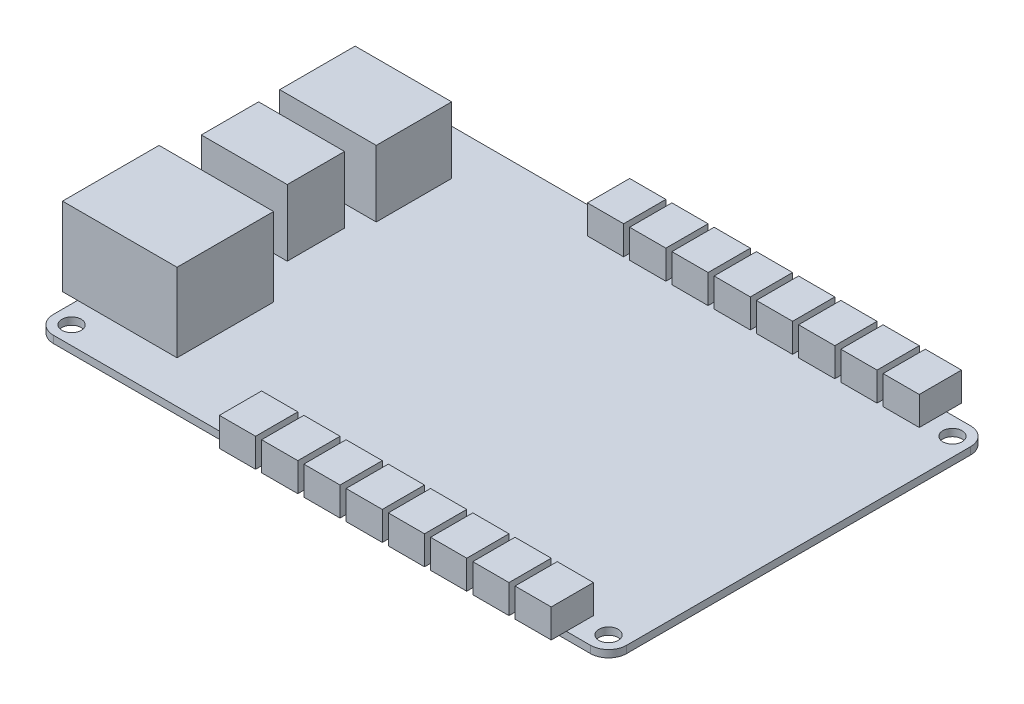
SolidWorks part; units mm, degrees
ref_plane "Front Plane" through (0, 0, 0) normal (0, 0, 1) x (1, 0, 0)
ref_plane "Top Plane" through (0, 0, 0) normal (0, 1, 0) x (1, 0, 0)
ref_plane "Right Plane" through (0, 0, 0) normal (1, 0, 0) x (0, 0, -1)
sketch "Sketch1" plane through (0, 0, 0) normal (0, 1, 0) x (1, 0, 0)
  line L1 (-54.7675, 6.7441) -> (34.2325, 6.7441)
  line L2 (-57.7675, 3.7441) -> (-57.7675, -53.2559)
  line L3 (-54.7675, -56.2559) -> (34.2325, -56.2559)
  line L4 (37.2325, 3.7441) -> (37.2325, -53.2559)
  arc A0 (-57.7675, -53.2559) -> (-54.7675, -56.2559) centre (-54.7675, -53.2559) ccw
  arc A1 (34.2325, -56.2559) -> (37.2325, -53.2559) centre (34.2325, -53.2559) ccw
  arc A2 (34.2325, 6.7441) -> (37.2325, 3.7441) centre (34.2325, 3.7441) cw
  arc A3 (-54.7675, 6.7441) -> (-57.7675, 3.7441) centre (-54.7675, 3.7441) ccw
  circle A4 centre (-54.7675, 3.7441) radius 1.6
  circle A5 centre (-54.7675, -53.2559) radius 1.6
  circle A6 centre (34.2325, -53.2559) radius 1.6
  circle A7 centre (34.2325, 3.7441) radius 1.6
  point P6 (-57.7675, -56.2559)
  point P9 (37.2325, -56.2559)
  point P14 (-57.7675, 6.7441)
  dimension "D3" = 3
  dimension "D4" = 3.2
  dimension "D5" = 3.2
  dimension "D6" = 3.2
  dimension "D7" = 3.2
  dimension "D1" = 95
  dimension "D2" = 63
extrude "pcb" add sketch "Sketch1" along normal blind 1.2
sketch "Sketch2" plane through (0, 1.2, 0) normal (0, 1, 0) x (1, 0, 0)
  line L0 (-17.7675, -51.7559) -> (-17.7675, -58.7559)
  line L1 (-24.7675, -51.7559) -> (-18.7675, -51.7559)
  line L2 (-24.7675, -51.7559) -> (-24.7675, -58.7559)
  line L3 (-24.7675, -58.7559) -> (-18.7675, -58.7559)
  line L4 (-18.7675, -51.7559) -> (-18.7675, -58.7559)
  line L5 (-17.7675, -51.7559) -> (-11.7675, -51.7559)
  line L6 (-11.7675, -51.7559) -> (-11.7675, -58.7559)
  line L7 (-17.7675, -58.7559) -> (-11.7675, -58.7559)
  line L8 (-10.7675, -51.7559) -> (-10.7675, -58.7559)
  line L9 (-10.7675, -51.7559) -> (-4.7675, -51.7559)
  line L10 (-4.7675, -51.7559) -> (-4.7675, -58.7559)
  line L11 (-10.7675, -58.7559) -> (-4.7675, -58.7559)
  line L12 (-3.7675, -51.7559) -> (-3.7675, -58.7559)
  line L13 (-3.7675, -51.7559) -> (2.2325, -51.7559)
  line L14 (2.2325, -51.7559) -> (2.2325, -58.7559)
  line L15 (-3.7675, -58.7559) -> (2.2325, -58.7559)
  line L16 (3.2325, -51.7559) -> (3.2325, -58.7559)
  line L17 (3.2325, -51.7559) -> (9.2325, -51.7559)
  line L18 (9.2325, -51.7559) -> (9.2325, -58.7559)
  line L19 (3.2325, -58.7559) -> (9.2325, -58.7559)
  line L20 (10.2325, -51.7559) -> (10.2325, -58.7559)
  line L21 (10.2325, -51.7559) -> (16.2325, -51.7559)
  line L22 (16.2325, -51.7559) -> (16.2325, -58.7559)
  line L23 (10.2325, -58.7559) -> (16.2325, -58.7559)
  line L24 (17.2325, -51.7559) -> (17.2325, -58.7559)
  line L25 (17.2325, -51.7559) -> (23.2325, -51.7559)
  line L26 (23.2325, -51.7559) -> (23.2325, -58.7559)
  line L27 (17.2325, -58.7559) -> (23.2325, -58.7559)
  line L28 (24.2325, -51.7559) -> (24.2325, -58.7559)
  line L29 (24.2325, -51.7559) -> (30.2325, -51.7559)
  line L30 (30.2325, -51.7559) -> (30.2325, -58.7559)
  line L31 (24.2325, -58.7559) -> (30.2325, -58.7559)
  line L32 (-57.7675, 3.7441) -> (-57.7675, -53.2559) construction
  line L33 (-54.7675, -56.2559) -> (34.2325, -56.2559) construction
  line L34 (-57.7675, -24.7559) -> (37.2325, -24.7559) construction
  line L35 (37.2325, -53.2559) -> (37.2325, 3.7441) construction
  line L36 (24.2325, 9.2441) -> (30.2325, 9.2441)
  line L37 (30.2325, 2.2441) -> (30.2325, 9.2441)
  line L38 (24.2325, 2.2441) -> (30.2325, 2.2441)
  line L39 (24.2325, 2.2441) -> (24.2325, 9.2441)
  line L40 (17.2325, 9.2441) -> (23.2325, 9.2441)
  line L41 (23.2325, 2.2441) -> (23.2325, 9.2441)
  line L42 (17.2325, 2.2441) -> (23.2325, 2.2441)
  line L43 (17.2325, 2.2441) -> (17.2325, 9.2441)
  line L44 (10.2325, 9.2441) -> (16.2325, 9.2441)
  line L45 (16.2325, 2.2441) -> (16.2325, 9.2441)
  line L46 (10.2325, 2.2441) -> (16.2325, 2.2441)
  line L47 (10.2325, 2.2441) -> (10.2325, 9.2441)
  line L48 (3.2325, 9.2441) -> (9.2325, 9.2441)
  line L49 (9.2325, 2.2441) -> (9.2325, 9.2441)
  line L50 (3.2325, 2.2441) -> (9.2325, 2.2441)
  line L51 (3.2325, 2.2441) -> (3.2325, 9.2441)
  line L52 (-3.7675, 9.2441) -> (2.2325, 9.2441)
  line L53 (2.2325, 2.2441) -> (2.2325, 9.2441)
  line L54 (-3.7675, 2.2441) -> (2.2325, 2.2441)
  line L55 (-3.7675, 2.2441) -> (-3.7675, 9.2441)
  line L56 (-10.7675, 9.2441) -> (-4.7675, 9.2441)
  line L57 (-4.7675, 2.2441) -> (-4.7675, 9.2441)
  line L58 (-10.7675, 2.2441) -> (-4.7675, 2.2441)
  line L59 (-10.7675, 2.2441) -> (-10.7675, 9.2441)
  line L60 (-17.7675, 9.2441) -> (-11.7675, 9.2441)
  line L61 (-11.7675, 2.2441) -> (-11.7675, 9.2441)
  line L62 (-17.7675, 2.2441) -> (-11.7675, 2.2441)
  line L63 (-18.7675, 2.2441) -> (-18.7675, 9.2441)
  line L64 (-24.7675, 9.2441) -> (-18.7675, 9.2441)
  line L65 (-24.7675, 2.2441) -> (-24.7675, 9.2441)
  line L66 (-24.7675, 2.2441) -> (-18.7675, 2.2441)
  line L67 (-17.7675, 2.2441) -> (-17.7675, 9.2441)
  dimension "D1" = 6
  dimension "D2" = 7
  dimension "D4" = 33
  dimension "D5" = 2.5
  dimension "D3" = 8
extrude "pop connectors" add sketch "Sketch2" along normal blind 4.75
sketch "usb" plane through (0, 1.2, 0) normal (0, 1, 0) x (1, 0, 0)
  line L0 (-54.7675, -56.2559) -> (-24.7675, -56.2559) construction
  line L1 (-60.2675, -0.7559) -> (-44.2675, -0.7559)
  line L2 (-60.2675, -0.7559) -> (-60.2675, -13.2559)
  line L3 (-60.2675, -13.2559) -> (-44.2675, -13.2559)
  line L4 (-44.2675, -0.7559) -> (-44.2675, -13.2559)
  line L5 (-57.7675, 3.7441) -> (-57.7675, -53.2559) construction
  dimension "D1" = 43
  dimension "D2" = 2.5
  dimension "D3" = 16
  dimension "D4" = 12.5
extrude "USB B" add sketch "usb" along normal blind 11
sketch "Sketch4" plane through (0, 1.2, 0) normal (0, 1, 0) x (1, 0, 0)
  line L0 (-54.7675, -56.2559) -> (-24.7675, -56.2559) construction
  line L1 (-60.2675, -16.7559) -> (-46.0175, -16.7559)
  line L2 (-60.2675, -16.7559) -> (-60.2675, -26.2559)
  line L3 (-60.2675, -26.2559) -> (-46.0175, -26.2559)
  line L4 (-46.0175, -16.7559) -> (-46.0175, -26.2559)
  line L5 (-57.7675, -13.2559) -> (-57.7675, -53.2559) construction
  dimension "D1" = 9.5
  dimension "D2" = 14.25
  dimension "D3" = 30
  dimension "D4" = 2.5
extrude "DC power" add sketch "Sketch4" along normal blind 11
sketch "Sketch5" plane through (0, 1.2, 0) normal (0, 1, 0) x (1, 0, 0)
  line L0 (-54.7675, -56.2559) -> (-24.7675, -56.2559) construction
  line L1 (-60.2675, -33.2559) -> (-41.2852, -33.2559)
  line L2 (-60.2675, -33.2559) -> (-60.2675, -49.2559)
  line L3 (-60.2675, -49.2559) -> (-41.2852, -49.2559)
  line L4 (-41.2852, -33.2559) -> (-41.2852, -49.2559)
  line L5 (-57.7675, -26.2559) -> (-57.7675, -53.2559) construction
  dimension "D1" = 16
  dimension "D2" = 7
  dimension "D3" = 2.5
extrude "RJ45" add sketch "Sketch5" along normal blind 13
